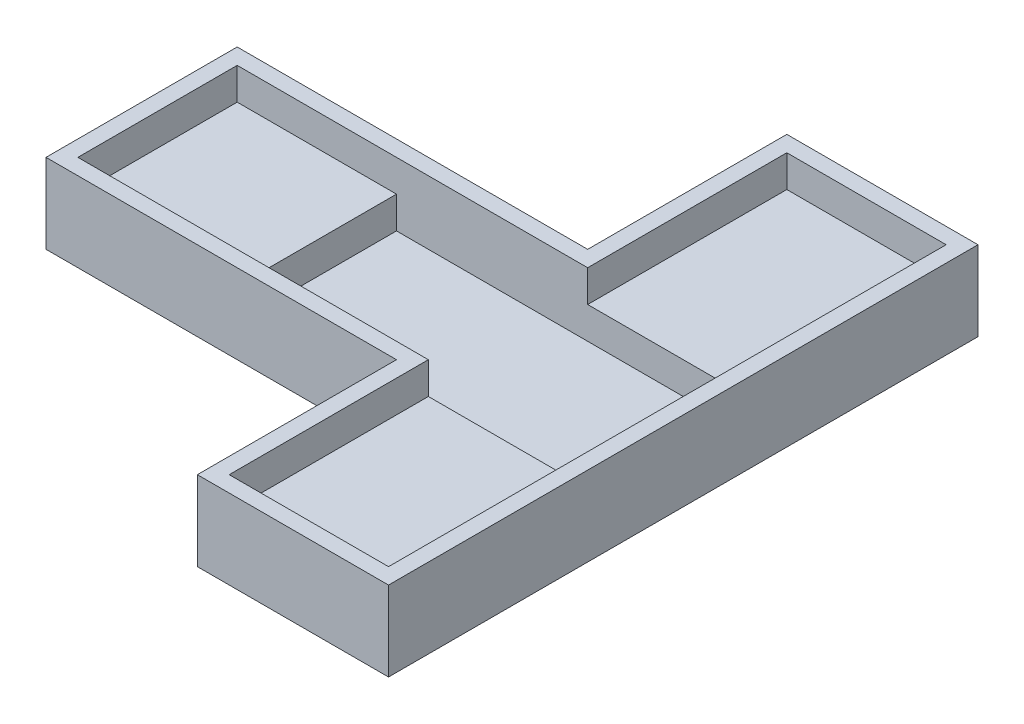
SolidWorks part; units mm, degrees
ref_plane "前视基准面" through (0, 0, 0) normal (0, 0, 1) x (1, 0, 0)
ref_plane "上视基准面" through (0, 0, 0) normal (0, 1, 0) x (1, 0, 0)
ref_plane "右视基准面" through (0, 0, 0) normal (1, 0, 0) x (0, 0, -1)
other "Configuration Table"
sketch "草图1" plane through (0, 0, 0) normal (0, 1, 0) x (1, 0, 0)
  line L1 (-11, -5) -> (11, -5)
  line L2 (-11, -5) -> (-11, 5)
  line L3 (-11, 5) -> (11, 5)
  line L4 (11, -5) -> (11, 5)
  line L5 (-11, -5) -> (11, 5) construction
  line L6 (-11, 5) -> (11, -5) construction
  line L7 (11, -5) -> (1, -5)
  line L8 (11, -5) -> (11, -17.5)
  line L9 (11, -17.5) -> (1, -17.5)
  line L10 (1, -5) -> (1, -17.5)
  line L11 (11, 5) -> (1, 5)
  line L12 (11, 5) -> (11, 17.5)
  line L13 (11, 17.5) -> (1, 17.5)
  line L14 (1, 5) -> (1, 17.5)
  line L15 (-11, 5) -> (-21, 5)
  line L16 (-11, 5) -> (-11, -5)
  line L17 (-11, -5) -> (-21, -5)
  line L18 (-21, 5) -> (-21, -5)
  point P0 (0, 0)
  dimension "D1" = 22
  dimension "D2" = 10
  dimension "D3" = 10
  dimension "D4" = 10
  dimension "D5" = 12.5
  dimension "D6" = 12.5
  dimension "D7" = 10
sketch "草图2" plane through (0, 0, 0) normal (0, 1, 0) x (1, 0, 0)
  line L1 (-21, 5) -> (11, 5)
  line L2 (-21, 5) -> (-21, -5)
  line L3 (-21, -5) -> (11, -5)
  line L4 (11, 5) -> (11, -5)
  line L5 (11, -17.5) -> (1, -17.5)
  line L6 (11, -17.5) -> (11, -5)
  line L7 (11, -5) -> (1, -5)
  line L8 (1, -17.5) -> (1, -5)
  line L9 (1, 5) -> (11, 5)
  line L10 (1, 5) -> (1, 17.5)
  line L11 (1, 17.5) -> (11, 17.5)
  line L12 (11, 5) -> (11, 17.5)
extrude "凸台-拉伸1" add sketch "草图2" along normal blind 1 contours L4 L1 L2 L3 | L1 L12 L11 L10 | L8 L5 L6 L3
sketch "草图3" plane through (0, 1, 0) normal (0, 1, 0) x (1, 0, 0)
  line L0 (12, -18.5) -> (12, 18.5)
  line L1 (12, 18.5) -> (0, 18.5)
  line L2 (0, 18.5) -> (0, 6)
  line L3 (0, 6) -> (-22, 6)
  line L4 (-22, 6) -> (-22, -6)
  line L5 (-22, -6) -> (0, -6)
  line L6 (0, -6) -> (0, -18.5)
  line L7 (0, -18.5) -> (12, -18.5)
  line L8 (11, -17.5) -> (11, 17.5)
  line L9 (11, 17.5) -> (1, 17.5)
  line L10 (1, 17.5) -> (1, 5)
  line L11 (1, 5) -> (-21, 5)
  line L12 (-21, 5) -> (-21, -5)
  line L13 (-21, -5) -> (1, -5)
  line L14 (1, -5) -> (1, -17.5)
  line L15 (1, -17.5) -> (11, -17.5)
  line L16 (11, -17.5) -> (11, 17.5)
  line L17 (11, 17.5) -> (1, 17.5)
  line L18 (1, 17.5) -> (1, 5)
  line L19 (1, 5) -> (-21, 5)
  line L20 (-21, 5) -> (-21, -5)
  line L21 (-21, -5) -> (1, -5)
  line L22 (1, -5) -> (1, -17.5)
  line L23 (1, -17.5) -> (11, -17.5)
  dimension "D1" = 0
  dimension "D2" = 1
extrude "凸台-拉伸2" add sketch "草图3" along normal blind 4 and the other way blind 1
sketch "草图4" plane through (0, 1, 0) normal (0, 1, 0) x (1, 0, 0)
  line L1 (-21, 5) -> (-11, 5)
  line L2 (-21, 5) -> (-21, -5)
  line L3 (-21, -5) -> (-11, -5)
  line L4 (-11, 5) -> (-11, -5)
  line L5 (1, 5) -> (11, 5)
  line L6 (1, 5) -> (1, 17.5)
  line L7 (1, 17.5) -> (11, 17.5)
  line L8 (11, 5) -> (11, 17.5)
  line L9 (1, -5) -> (11, -5)
  line L10 (1, -5) -> (1, -17.5)
  line L11 (1, -17.5) -> (11, -17.5)
  line L12 (11, -5) -> (11, -17.5)
extrude "凸台-拉伸3" add sketch "草图4" along normal blind 2
